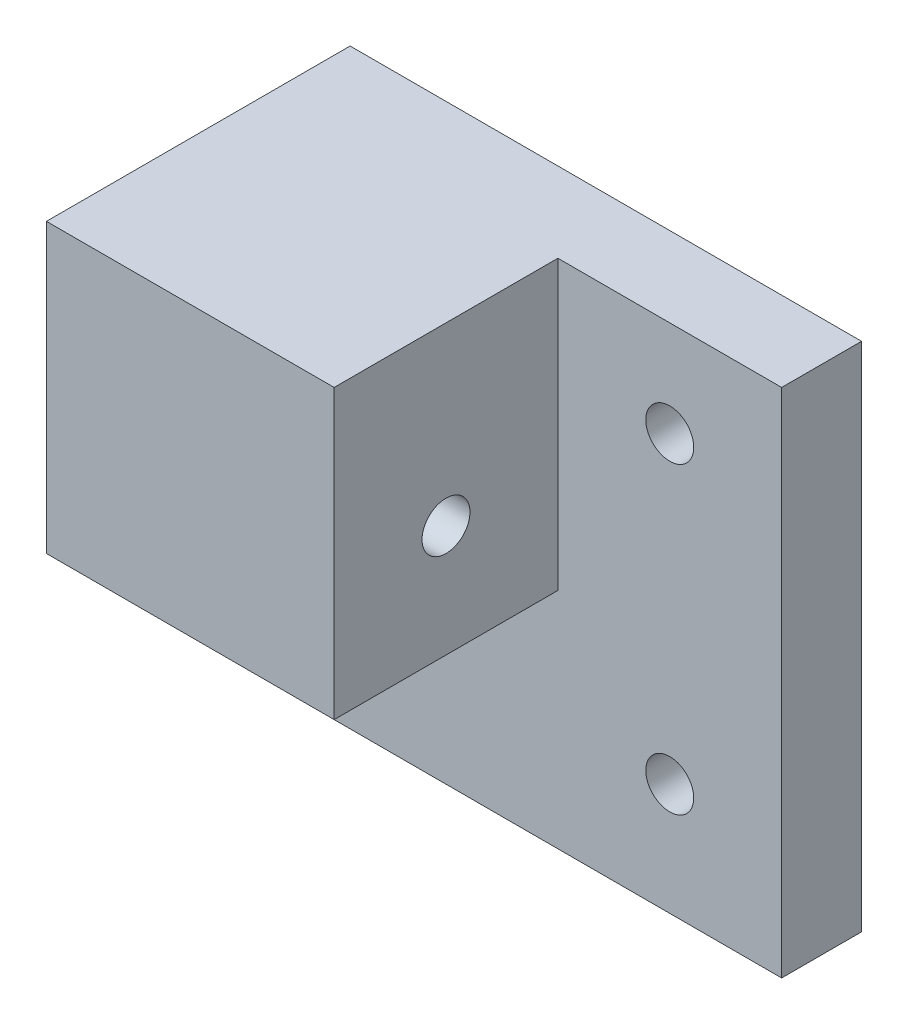
SolidWorks part; units mm, degrees
ref_plane "Ön Düzlem" through (0, 0, 0) normal (0, 0, 1) x (1, 0, 0)
ref_plane "Üst Düzlem" through (0, 0, 0) normal (0, 1, 0) x (1, 0, 0)
ref_plane "Sağ Düzlem" through (0, 0, 0) normal (1, 0, 0) x (0, 0, -1)
sketch "Çizim1" plane through (0, 0, 0) normal (0, 0, 1) x (1, 0, 0)
  line L1 (0, 0) -> (-64, 0)
  line L2 (0, 0) -> (0, -64)
  line L3 (0, -64) -> (-64, -64)
  line L4 (-64, 0) -> (-64, -64)
  dimension "D1" = 64
  dimension "D2" = 64
extrude "Yükseklik-Ekstrüzyon1" add sketch "Çizim1" along normal blind 10
sketch "Çizim2" plane through (0, 0, 10) normal (0, 0, 1) x (1, 0, 0)
  line L0 (0, -64) -> (0, 0) construction
  line L1 (-64, 0) -> (-28, 0)
  line L2 (-64, 0) -> (-64, -36)
  line L3 (-64, -36) -> (-28, -36)
  line L4 (-28, 0) -> (-28, -36)
  line L5 (-64, -64) -> (0, -64) construction
  dimension "D1" = 28
  dimension "D2" = 28
extrude "Yükseklik-Ekstrüzyon2" add sketch "Çizim2" along normal blind 28
sketch "Çizim3" plane through (0, -36, 0) normal (0, -1, 0) x (1, 0, 0)
  line L0 (0, 10) -> (0, 0) construction
  line L4 (-46, 38) -> (-46, 10) construction
  line L5 (-64, 38) -> (-28, 38) construction
  line L6 (-64, 10) -> (-28, 10) construction
  circle A0 centre (-42, 24) radius 3
  point P3 (-46, 24)
  dimension "D1" = 6
  dimension "D2" = 42
extrude "Kes-Ekstrüzyon1" cut sketch "Çizim3" against normal blind 20
sketch "Çizim4" plane through (-28, 0, 0) normal (1, 0, 0) x (0, 0, -1)
  line L0 (-10, -64) -> (0, -64) construction
  line L5 (-38, -18) -> (-10, -18) construction
  line L6 (-38, -36) -> (-38, 0) construction
  line L7 (-10, -36) -> (-10, 0) construction
  circle A0 centre (-24, -22) radius 3
  point P3 (-24, -18)
  dimension "D1" = 6
  dimension "D2" = 42
extrude "Kes-Ekstrüzyon2" cut sketch "Çizim4" against normal blind 20
sketch "Çizim5" plane through (0, 0, 10) normal (0, 0, 1) x (1, 0, 0)
  line L0 (0, -64) -> (0, 0) construction
  line L1 (-64, -64) -> (0, -64) construction
  line L2 (0, -64) -> (0, 0) construction
  circle A0 centre (-14, -50) radius 3
  circle A1 centre (-14, -12) radius 3
  circle A2 centre (-52, -50) radius 3
  point P12 (0, 0)
  point P13 (0, 0)
  dimension "D3" = 6
  dimension "D1" = 14
  dimension "D2" = 14
  dimension "D4" = 52
  dimension "D5" = 52
extrude "Kes-Ekstrüzyon3" cut sketch "Çizim5" against normal through all
